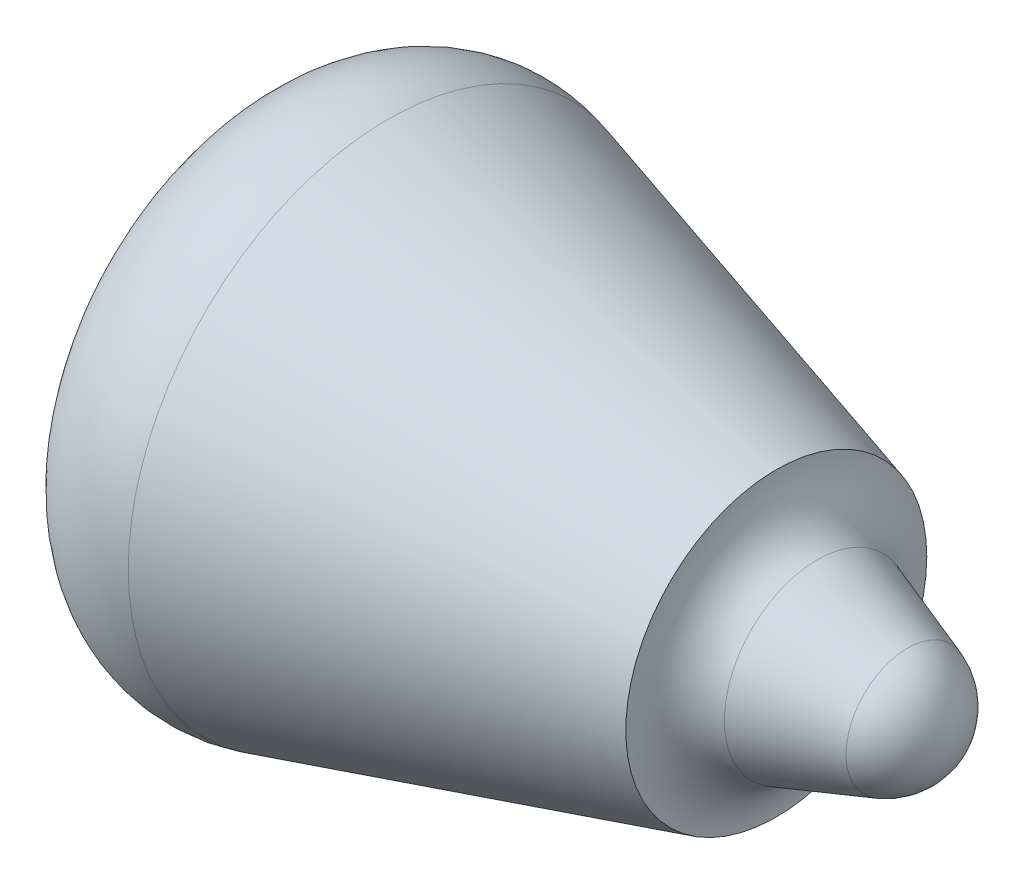
SolidWorks part; units mm, degrees
ref_plane "Alzado" through (0, 0, 0) normal (0, 0, 1) x (1, 0, 0)
ref_plane "Planta" through (0, 0, 0) normal (0, 1, 0) x (1, 0, 0)
ref_plane "Vista lateral" through (0, 0, 0) normal (1, 0, 0) x (0, 0, -1)
sketch "Croquis1" plane through (0, 0, 0) normal (0, 0, 1) x (1, 0, 0)
  line L0 (0, 111) -> (0, 0)
  line L1 (0, 0) -> (522, 0)
  line L2 (106.835, 191.8367) -> (393, 111)
  line L3 (423.2091, 68.5002) -> (489.777, 45.3331)
  arc A0 (106.835, 191.8367) -> (0, 111) centre (84, 111) ccw
  arc A1 (393, 111) -> (423.2091, 68.5002) centre (438, 111) ccw
  arc A2 (522, 0) -> (489.777, 45.3331) centre (474, 0) ccw
  point P14 (389.7008, 31.7869)
  point P15 (141.407, 51.4537)
  point P16 (341.3532, 30.148)
  point P17 (31.6005, 225.1774)
  point P18 (238.1023, 175.1909)
  point P19 (225.8105, 112.9126)
  point P20 (209.4215, 101.4403)
  point P21 (231.5466, 148.149)
  point P22 (96.3371, 262.8722)
  point P23 (277.4359, 185.0243)
  point P24 (61.6689, 323.5116)
  point P25 (0, 0)
  point P26 (357.5493, 111)
  point P27 (208.5799, 81.0975)
  point P28 (0, 0)
  point P29 (0, 0)
  dimension "D1" = 111
  dimension "D3" = 96
  dimension "D4" = 90
  dimension "D5" = 168
  dimension "D2" = 522
  dimension "D6" = 438
  dimension "D7" = 111
revolve "Revolución1" add sketch "Croquis1" angle 360 about L1
sketch "Croquis3" plane through (0, 0, 0) normal (0, 0, 1) x (1, 0, 0)
  arc A0 (139.718, 111.6812) -> (329.474, -29.7921) centre (357.3295, 205.5653) ccw
  arc A1 (178.5926, 127.5586) -> (331.0882, 29.939) centre (321.3383, 182.6281) ccw
  arc A2 (178.5926, 127.5586) -> (139.718, 111.6812) centre (159, 120) ccw
  arc A3 (329.474, -29.7921) -> (331.0882, 29.939) centre (333, 0) ccw
  point P9 (0, 0)
  dimension "D1" = 42
  dimension "D2" = 60
  dimension "D3" = 474
  dimension "D4" = 306
  dimension "D5" = 120
  dimension "D6" = 333
  dimension "D7" = 174
